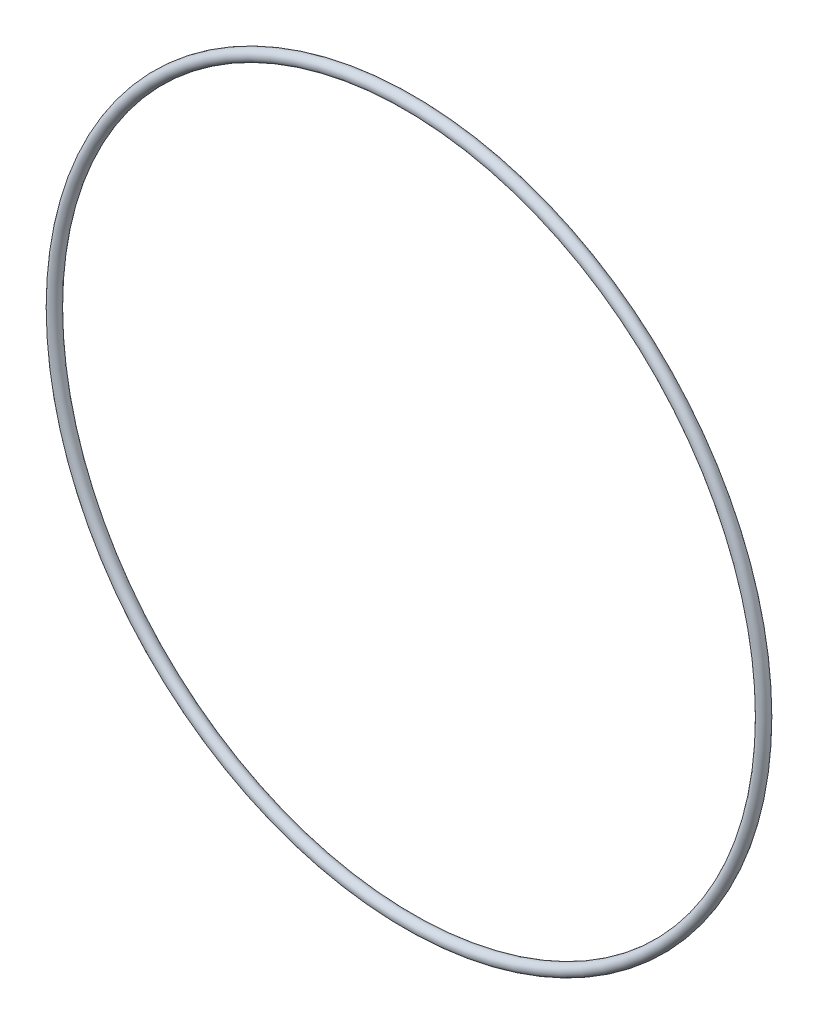
SolidWorks part; units mm, degrees
ref_plane "Front Plane" through (0, 0, 0) normal (0, 0, 1) x (1, 0, 0)
ref_plane "Top Plane" through (0, 0, 0) normal (0, 1, 0) x (1, 0, 0)
ref_plane "Right Plane" through (0, 0, 0) normal (1, 0, 0) x (0, 0, -1)
sketch "Sketch1" plane through (0, 0, 0) normal (0, 0, 1) x (1, 0, 0)
  circle A0 centre (0, 0) radius 30.5
  dimension "D1" = 61
sweep "Sweep1" add path "Sketch1" circular profile diameter 1 parameters "D3"=1
